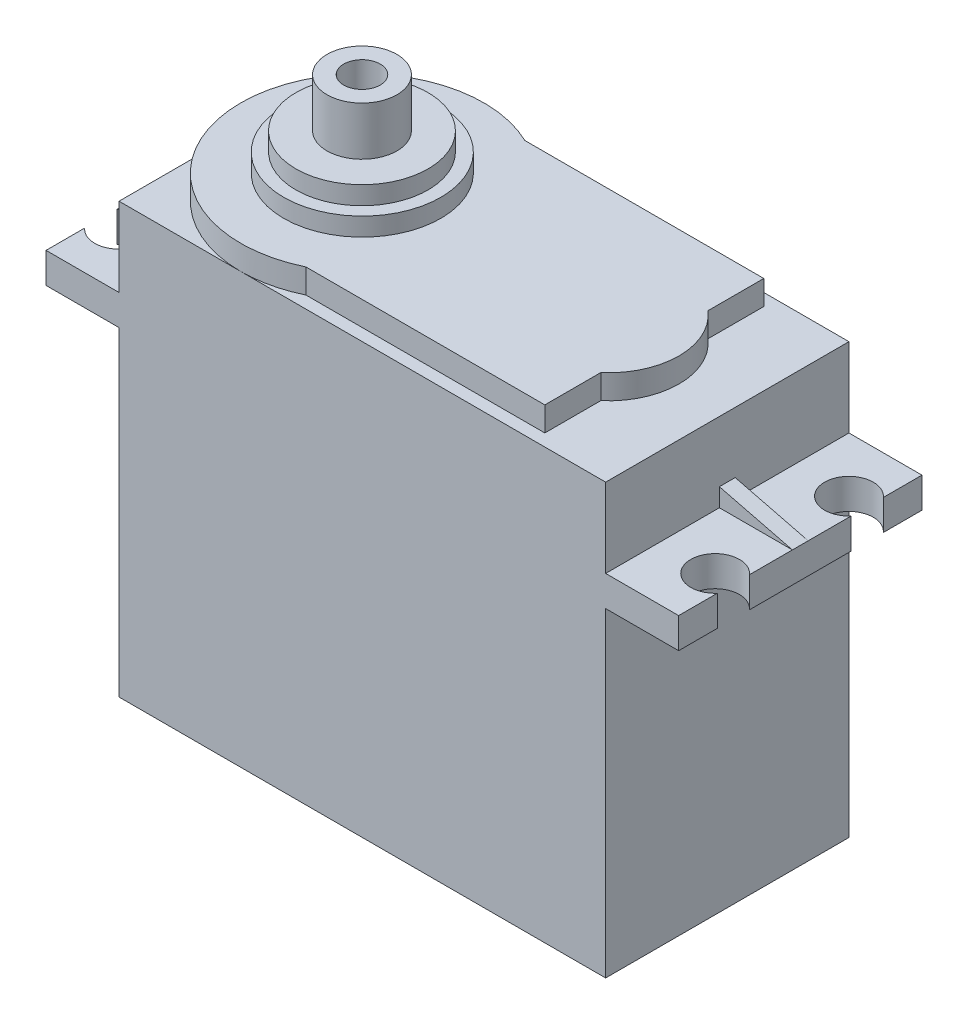
SolidWorks part; units mm, degrees
ref_plane "Front Plane" through (0, 0, 0) normal (0, 0, 1) x (1, 0, 0)
ref_plane "Top Plane" through (0, 0, 0) normal (0, 1, 0) x (1, 0, 0)
ref_plane "Right Plane" through (0, 0, 0) normal (1, 0, 0) x (0, 0, -1)
sketch "Sketch1" plane through (0, 0, 0) normal (0, 1, 0) x (1, 0, 0)
  line L1 (0, 0) -> (40, 0)
  line L2 (0, 0) -> (0, 20)
  line L3 (0, 20) -> (40, 20)
  line L4 (40, 0) -> (40, 20)
  dimension "D1" = 40
  dimension "D2" = 20
extrude "Boss-Extrude1" add sketch "Sketch1" along normal blind 35.3
sketch "Sketch2" plane through (0, 35.3, 0) normal (0, 1, 0) x (1, 0, 0)
  line L0 (0, 10) -> (36, 10) construction
  line L1 (0, 20) -> (0, 0) construction
  line L2 (0.001, 10) -> (0, 10)
  line L3 (36, 10) -> (34, 10) construction
  line L4 (34, 14.4006) -> (34, 19)
  line L5 (34, 5.5994) -> (34, 1)
  line L6 (40, 20) -> (0, 20) construction
  line L7 (0, 0) -> (40, 0) construction
  line L8 (34, 19) -> (14.3599, 19)
  line L9 (34, 1) -> (14.3599, 1)
  arc A0 (14.3599, 19) -> (14.3599, 1) centre (10.001, 10) ccw
  arc A1 (34, 5.5994) -> (34, 14.4006) centre (30.2486, 10) ccw
  dimension "D1" = 36
  dimension "D2" = 0.001
  dimension "D3" = 2
  dimension "D4" = 1
  dimension "D5" = 1
extrude "Boss-Extrude2" add sketch "Sketch2" along normal blind 2 contours L5 A1 L4 L8 A0 L9
sketch "Sketch3" plane through (0, 37.3, 0) normal (0, 1, 0) x (1, 0, 0)
  line L0 (0.001, 10) -> (40, 10) construction
  line L1 (40, 0) -> (40, 20) construction
  arc A0 (14.3599, 19) -> (14.3599, 1) centre (10.001, 10) ccw construction
  circle A1 centre (9.9932, 10) radius 9.9586
  circle A2 centre (9.9932, 10) radius 6.4586
  dimension "D1" = 3.5
extrude "Boss-Extrude3" add sketch "Sketch3" along normal blind 1.5 contours A2
sketch "Sketch4" plane through (0, 38.8, 0) normal (0, 1, 0) x (1, 0, 0)
  line L0 (0.001, 10) -> (40, 10) construction
  line L1 (40, 0) -> (40, 20) construction
  arc A0 (14.3599, 19) -> (14.3599, 1) centre (10.001, 10) ccw construction
  circle A1 centre (9.9702, 10) radius 6.4334
  circle A2 centre (9.9702, 10) radius 5.4334
  dimension "D1" = 1
extrude "Boss-Extrude4" add sketch "Sketch4" along normal blind 1.5 contours A2
sketch "Sketch5" plane through (0, 40.3, 0) normal (0, 1, 0) x (1, 0, 0)
  line L0 (4.5368, 10) -> (15.4037, 10) construction
  line L1 (9.9702, 15.4334) -> (9.9702, 4.5666) construction
  circle A0 centre (9.9702, 10) radius 5.4334 construction
  circle A1 centre (9.9702, 10) radius 5.4334 construction
  circle A2 centre (9.9702, 10) radius 2.875
  dimension "D1" = 5.75
extrude "Boss-Extrude5" add sketch "Sketch5" along normal blind 4 contours A2
sketch "Sketch6" plane through (40, 0, 0) normal (1, 0, 0) x (0, 0, -1)
  line L0 (0, 35.3) -> (0, 0) construction
  line L1 (0, 28.8) -> (20, 28.8)
  line L2 (0, 28.8) -> (0, 26.3)
  line L3 (0, 26.3) -> (20, 26.3)
  line L4 (20, 28.8) -> (20, 26.3)
  line L5 (20, 35.3) -> (20, 0) construction
  line L6 (0, 35.3) -> (20, 35.3) construction
  dimension "D1" = 9
  dimension "D2" = 2.5
extrude "Boss-Extrude6" add sketch "Sketch6" along normal blind 6
sketch "Sketch7" plane through (0, 28.8, 0) normal (0, 1, 0) x (1, 0, 0)
  line L0 (46, 15.5) -> (40, 15.5) construction
  line L1 (46, 20) -> (46, 0) construction
  line L2 (40, 20) -> (40, 0) construction
  line L3 (46, 4.5) -> (40, 4.5) construction
  line L4 (42.5, 4.5) -> (40, 4.5)
  line L5 (40, 15.5) -> (43, 15.5) construction
  line L6 (44.5, 17.5) -> (44.5, 20) construction
  line L7 (46, 20) -> (40, 20) construction
  line L8 (44.5, 2.5) -> (44.5, 0) construction
  line L9 (46, 0) -> (40, 0) construction
  line L10 (40, 15.5) -> (42.5, 15.5)
  circle A0 centre (44.5, 4.5) radius 2
  circle A1 centre (44.5, 15.5) radius 2
  line M8 (46, 0) -> (46, 20)
  dimension "D1" = 4
  dimension "D2" = 4
  dimension "D3" = 2.5
  dimension "D4" = 2.5
  dimension "D5" = 2.5
  dimension "D6" = 2.5
extrude "Cut-Extrude1" cut sketch "Sketch7" against normal blind 7 contours A0 M8 | A1 M8
sketch "Sketch8" plane through (0, 0, 0) normal (-1, 0, 0) x (0, 0, 1)
  line L0 (-20, 35.3) -> (-20, 0) construction
  line L1 (-20, 28.8) -> (0, 28.8)
  line L2 (-20, 28.8) -> (-20, 26.3)
  line L3 (-20, 26.3) -> (0, 26.3)
  line L4 (0, 28.8) -> (0, 26.3)
  line L5 (0, 35.3) -> (0, 0) construction
  line L6 (-20, 35.3) -> (0, 35.3) construction
  dimension "D1" = 9
  dimension "D2" = 2.5
extrude "Boss-Extrude7" add sketch "Sketch8" along normal blind 6
sketch "Sketch9" plane through (0, 28.8, 0) normal (0, 1, 0) x (1, 0, 0)
  line L0 (-6, 15.5) -> (-1.7305, 15.5) construction
  line L1 (-6, 0) -> (-6, 20) construction
  line L2 (-6, 4.5) -> (-1.2323, 4.5) construction
  line L3 (-2.5, 15.5) -> (0, 15.5) construction
  line L4 (0, 0) -> (0, 20) construction
  line L5 (-2.5, 4.5) -> (0, 4.5)
  line L6 (0, 20) -> (0, 0) construction
  line L7 (-4.5, 2.5) -> (-4.5, 0) construction
  line L8 (-6, 0) -> (0, 0) construction
  line L9 (-4.5, 17.5) -> (-4.5, 20) construction
  line L10 (-6, 20) -> (0, 20) construction
  circle A0 centre (-4.5, 15.5) radius 2
  circle A1 centre (-4.5, 4.5) radius 2
  line M5 (-6, 20) -> (-6, 0)
  dimension "D1" = 4
  dimension "4" = 4
  dimension "D2" = 2.5
  dimension "D3" = 2.5
  dimension "D4" = 2.5
  dimension "D5" = 2.5
extrude "Cut-Extrude2" cut sketch "Sketch9" against normal blind 7 contours A0 M5 | A1 M5
sketch "Sketch11" plane through (0, 0, 0) normal (-1, 0, 0) x (0, 0, 1)
  line L0 (-20, 0) -> (0, 0) construction
  line L1 (-13.7251, 10.7) -> (-6.7251, 10.7)
  line L2 (-13.7251, 10.7) -> (-13.7251, 6.7)
  line L3 (-13.7251, 6.7) -> (-6.7251, 6.7)
  line L4 (-6.7251, 10.7) -> (-6.7251, 6.7)
  dimension "D1" = 4
  dimension "D2" = 7
  dimension "D3" = 6.7
extrude "Boss-Extrude8" add sketch "Sketch11" along normal blind 6 contours L2 L1 L4 L3
sketch "Sketch12" plane through (-6, 0, 0) normal (-1, 0, 0) x (0, 0, 1)
  line L0 (-13.7251, 10.7) -> (-6.7251, 10.7) construction
  line L1 (-13.4751, 10.45) -> (-6.9751, 10.45)
  line L2 (-13.4751, 10.45) -> (-13.4751, 6.95)
  line L3 (-13.4751, 6.95) -> (-6.9751, 6.95)
  line L4 (-6.9751, 10.45) -> (-6.9751, 6.95)
  line L5 (-6.7251, 10.7) -> (-6.7251, 6.7) construction
  line L7 (-13.7251, 10.7) -> (-13.7251, 6.7) construction
  line L8 (-13.7251, 6.7) -> (-6.7251, 6.7) construction
  dimension "D1" = 0.25
  dimension "D2" = 0.25
  dimension "D3" = 0.25
  dimension "D4" = 0.25
extrude "Cut-Extrude3" cut sketch "Sketch12" against normal blind 6 contours L2 L1 L4 L3
sketch "Sketch13" plane through (0, 28.8, 0) normal (0, 1, 0) x (1, 0, 0)
  line L0 (46, 10) -> (40, 10) construction
  line L1 (46, 14.1771) -> (46, 5.8229) construction
  line L2 (40, 0) -> (40, 20) construction
  line L3 (40, 20) -> (40, 0) construction
  line L4 (40, 10.65) -> (46, 10.65)
  line L5 (40, 10.65) -> (40, 9.35)
  line L6 (40, 9.35) -> (46, 9.35)
  line L7 (46, 10.65) -> (46, 9.35)
  dimension "D1" = 0.65
  dimension "D2" = 0.65
extrude "Boss-Extrude9" add sketch "Sketch13" along normal blind 1.5 contours L5 L4 L7 L6
sketch "Sketch14" plane through (0, 28.8, 0) normal (0, 1, 0) x (1, 0, 0)
  line L0 (-6, 10) -> (0, 10) construction
  line L1 (-6, 5.8229) -> (-6, 14.1771) construction
  line L2 (0, 0) -> (0, 20) construction
  line L4 (-6, 10.65) -> (0, 10.65)
  line L5 (-6, 10.65) -> (-6, 9.35)
  line L6 (-6, 9.35) -> (0, 9.35)
  line L7 (0, 10.65) -> (0, 9.35)
  dimension "D1" = 0.65
  dimension "D2" = 0.65
extrude "Boss-Extrude10" add sketch "Sketch14" along normal blind 1.5 contours L5 L4 L7 L6
sketch "Sketch15" plane through (0, 0, -9.35) normal (0, 0, 1) x (1, 0, 0)
  line L0 (40, 30.3) -> (46, 28.8)
  line L1 (46, 28.8) -> (46, 30.3)
  line L2 (46, 30.3) -> (40, 30.3)
extrude "Cut-Extrude4" cut sketch "Sketch15" against normal blind 1.5
sketch "Sketch16" plane through (0, 0, -9.35) normal (0, 0, 1) x (1, 0, 0)
  line L0 (-6, 28.8) -> (-6, 30.3)
  line L1 (-6, 30.3) -> (0, 30.3)
  line L2 (0, 30.3) -> (-6, 28.8)
extrude "Cut-Extrude5" cut sketch "Sketch16" against normal blind 1.5
sketch "Sketch17" plane through (0, 44.3, 0) normal (0, 1, 0) x (1, 0, 0)
  circle A0 centre (9.9702, 10) radius 1.5
  dimension "D1" = 3
extrude "Cut-Extrude6" cut sketch "Sketch17" against normal blind 4 contours A0
sketch "Sketch19" plane through (0, 40.3, 0) normal (0, 1, 0) x (1, 0, 0)
  circle A0 centre (9.9702, 10) radius 60.6171
